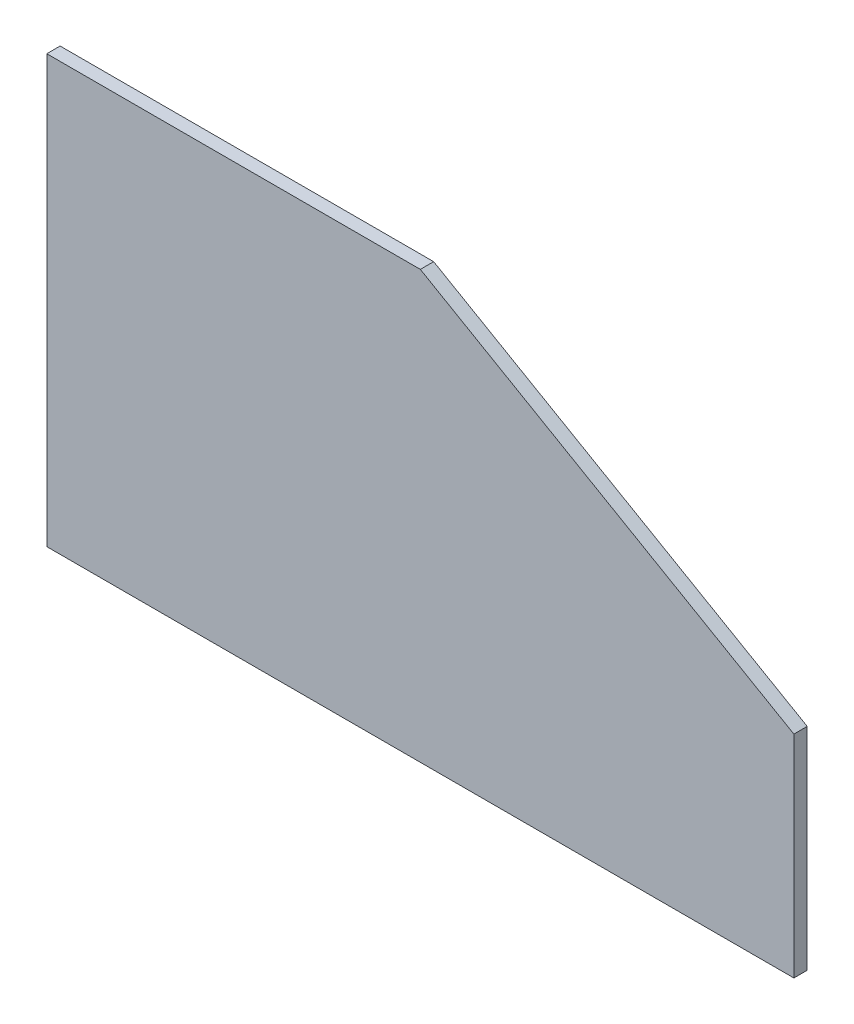
SolidWorks part; units mm, degrees
ref_plane "Front Plane" through (0, 0, 0) normal (0, 0, 1) x (1, 0, 0)
ref_plane "Top Plane" through (0, 0, 0) normal (0, 1, 0) x (1, 0, 0)
ref_plane "Right Plane" through (0, 0, 0) normal (1, 0, 0) x (0, 0, -1)
sketch "Sketch1" plane through (0, 0, 0) normal (0, 0, 1) x (1, 0, 0)
  line L0 (0, 0) -> (0, 203.2)
  line L1 (0, 203.2) -> (177.8, 203.2)
  line L2 (177.8, 203.2) -> (355.6, 100.5471)
  line L3 (355.6, 0) -> (0, 0)
  line L4 (355.6, 100.5471) -> (355.6, 0)
  line L6 (177.8, 0) -> (177.8, 203.2) construction
  dimension "D1" = 355.6
  dimension "D2" = 203.2
  dimension "D3" = 150
extrude "Boss-Extrude1" add sketch "Sketch1" along normal blind 6.35
